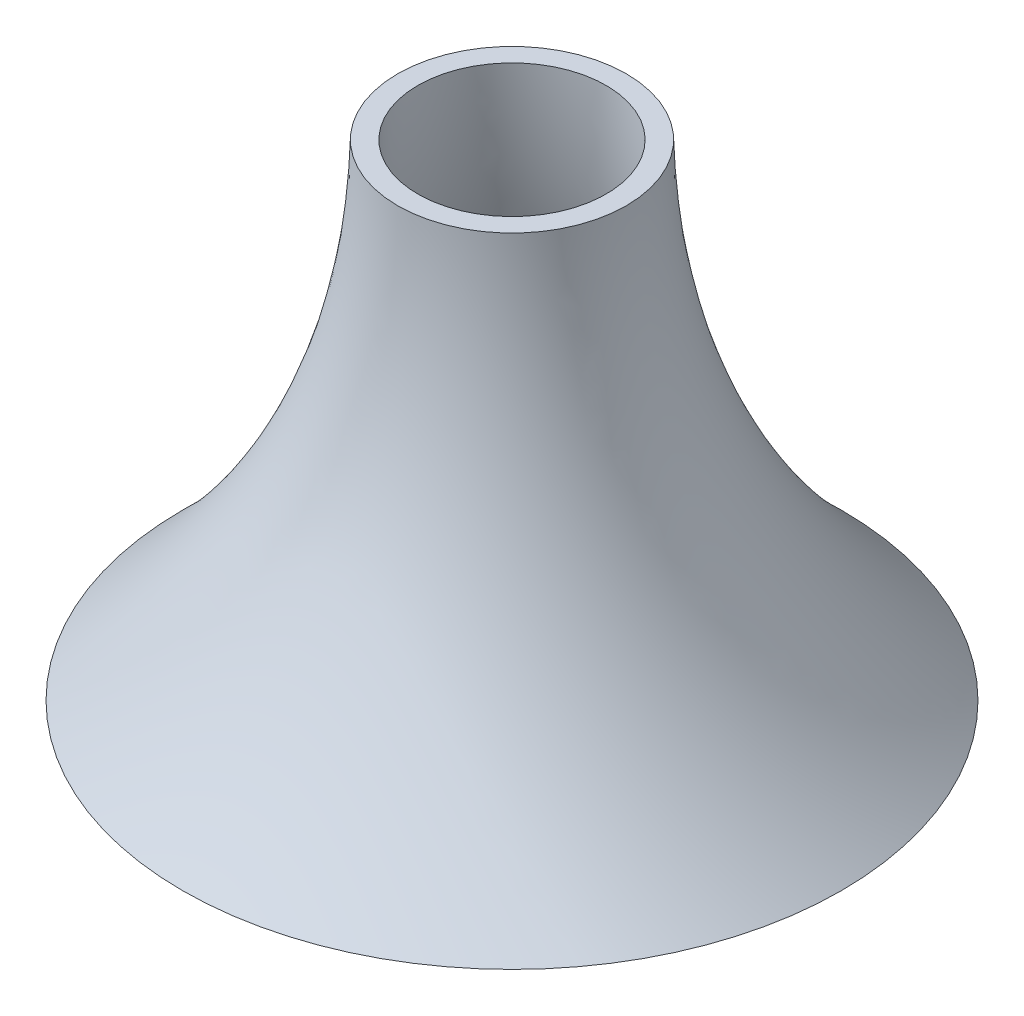
SolidWorks part; units mm, degrees
ref_plane "Front Plane" through (0, 0, 0) normal (0, 0, 1) x (1, 0, 0)
ref_plane "Top Plane" through (0, 0, 0) normal (0, 1, 0) x (1, 0, 0)
ref_plane "Right Plane" through (0, 0, 0) normal (1, 0, 0) x (0, 0, -1)
sketch "Sketch2" plane through (0, 0, 0) normal (0, 0, 1) x (1, 0, 0)
  line L0 (0, 105.448) -> (0, -81.5961) construction
  line L1 (35, 98.4039) -> (42.5, 98.4039)
  line L2 (114.9989, -82.1012) -> (122.4989, -82.1012)
  spline S0 degree 2 poles (35, 98.4039) (37.5834, -8.431) (114.9989, -82.1012) knots 0 0 0 1 1 1
  spline S1 degree 2 poles (42.5, 98.4039) (45.0834, -8.431) (122.4989, -82.1012) knots 0 0 0 1 1 1
  dimension "D2" = 7.5
  dimension "D1" = 35
  dimension "D3" = 115
  dimension "D4" = 180
  dimension "D5" = 7.5
  dimension "D6" = 7.5
revolve "Revolve1" add sketch "Sketch2" angle 360 about L0
sketch "Sketch6" plane through (0, 0, 0) normal (1, 0, 0) x (0, 0, -1)
  line L0 (0, 119.7798) -> (0, -98.2547) construction
  line L1 (-80.7187, 13.89) -> (69.9078, 13.89) construction
  line L2 (-51.8376, 33.3479) -> (-33.3376, 33.3479)
  line L3 (-35, 98.4039) -> (-35, -94.8081) construction
  spline S0 degree 2 poles (-58.0995, 13.89) (-54.5579, 23.4873) (-51.8376, 33.3479) knots 0 0 0 1 1 1
  spline S1 degree 2 poles (-58.0995, 13.89) (-49.8151, 28.8395) (-33.3376, 33.3479) knots 0 0 0 1 1 1
  spline S2 degree 2 poles (-42.5, 98.4039) (-45.0834, -8.431) (-122.4989, -82.1012) knots 0 0 0 1 1 1 construction
  dimension "D1" = 18.5
